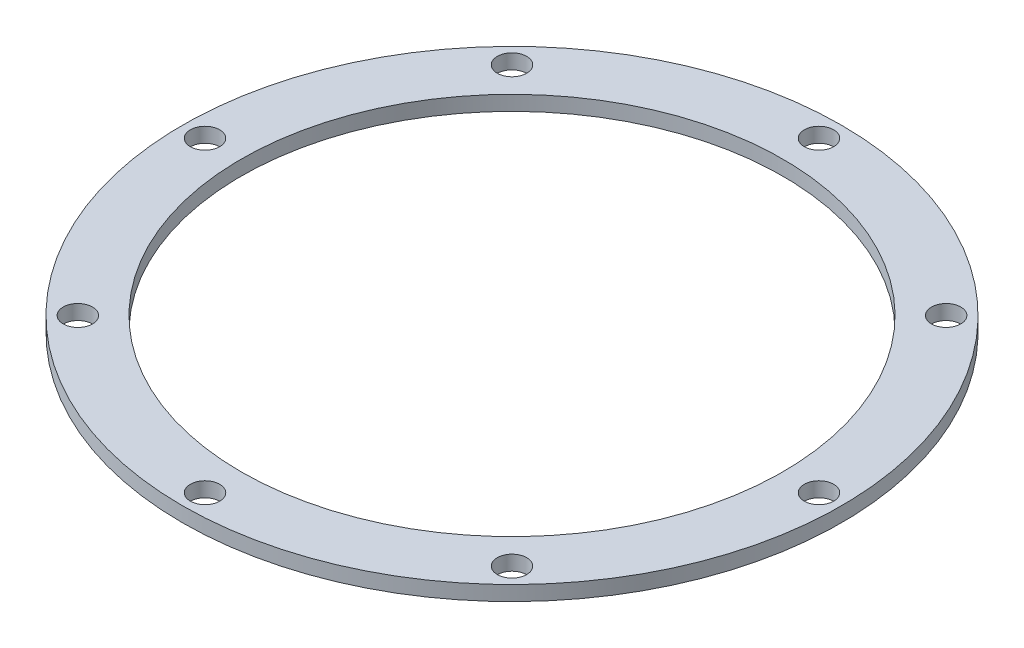
SolidWorks part; units mm, degrees
material "AISI 4130 Steel, normalized at 870C"
ref_plane "Front Plane" through (0, 0, 0) normal (0, 0, 1) x (1, 0, 0)
ref_plane "Top Plane" through (0, 0, 0) normal (0, 1, 0) x (1, 0, 0)
ref_plane "Right Plane" through (0, 0, 0) normal (1, 0, 0) x (0, 0, -1)
sketch "Sketch1" plane through (0, 0, 0) normal (0, 1, 0) x (1, 0, 0)
  circle A0 centre (0, 0) radius 73
  circle A1 centre (0, 0) radius 60
  circle A2 centre (-48.0833, 48.0833) radius 3.25
  circle A3 centre (-68, 0) radius 3.25
  circle A4 centre (0, 68) radius 3.25
  circle A5 centre (48.0833, 48.0833) radius 3.25
  circle A6 centre (68, 0) radius 3.25
  circle A7 centre (48.0833, -48.0833) radius 3.25
  circle A8 centre (0, -68) radius 3.25
  circle A9 centre (-48.0833, -48.0833) radius 3.25
  point P22 (0, 0)
  point P24 (0, 0)
  dimension "D1" = 146
  dimension "D2" = 120
  dimension "D3" = 68
  dimension "D4" = 6.5
  dimension "D5" = 8
extrude "Boss-Extrude1" add sketch "Sketch1" along normal blind 3.275
